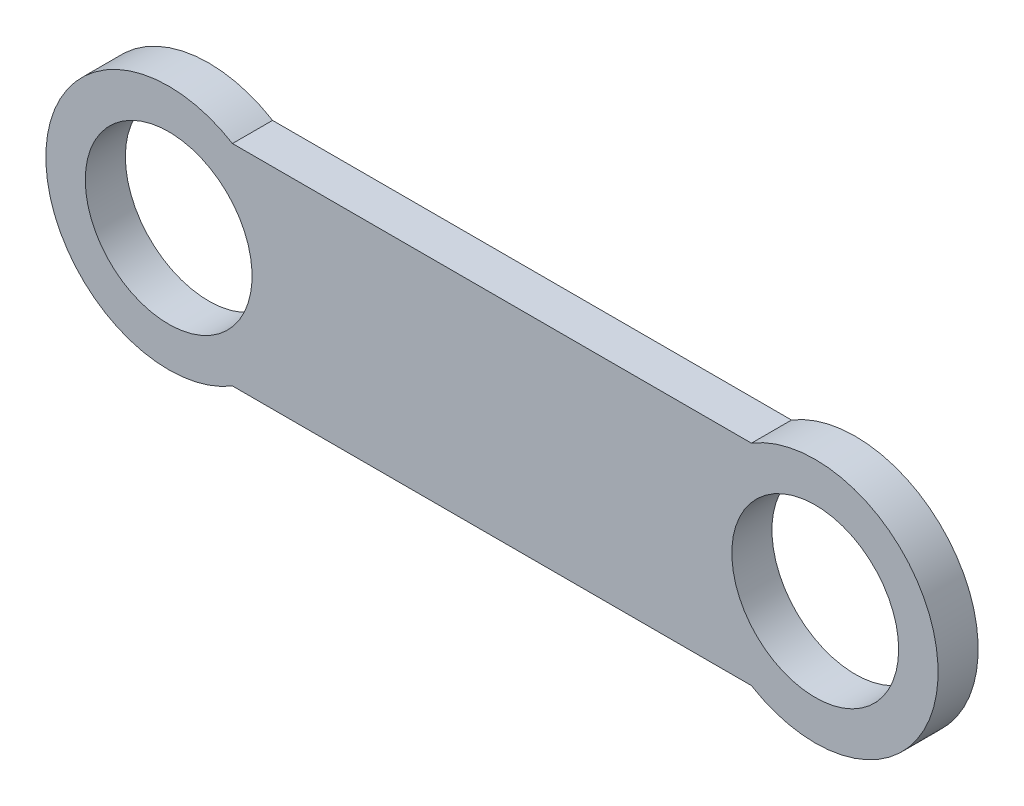
SolidWorks part; units mm, degrees
material "Teak"
ref_plane "Front Plane" through (0, 0, 0) normal (0, 0, 1) x (1, 0, 0)
ref_plane "Top Plane" through (0, 0, 0) normal (0, 1, 0) x (1, 0, 0)
ref_plane "Right Plane" through (0, 0, 0) normal (1, 0, 0) x (0, 0, -1)
sketch "Sketch1" plane through (0, 0, 0) normal (0, 0, 1) x (1, 0, 0)
  line L0 (-85.94, 0) -> (85.94, 0) construction
  line L1 (0, -39.678) -> (0, 39.678) construction
  line L2 (-20.0665, 8.1185) -> (20.0665, 8.1185)
  line L3 (-20.0665, -8.1185) -> (20.0665, -8.1185)
  circle A0 centre (25, 0) radius 6.45
  arc A1 (20.0665, 8.1185) -> (20.0665, -8.1185) centre (25, 0) cw
  arc A2 (-20.0665, 8.1185) -> (-20.0665, -8.1185) centre (-25, 0) ccw
  circle A3 centre (-25, 0) radius 6.45
  point P8 (0, 8.1185)
  point P12 (0, 0)
  point P16 (0, -8.1185)
  dimension "D1" = 9.5
  dimension "D2" = 12.9
  dimension "D3" = 50
extrude "Boss-Extrude1" add sketch "Sketch1" along normal blind 3.1 contours L2 A1 L3 A2
equation "\"p\"= 20mm"
equation "\"m\"= 1"
equation "\"hole_diam\"= 4mm"
equation "\"len_grip_1\" = 50mm"
equation "\"len_grip_2\" = 50mm"
equation "\"thick\" = 3.1mm"
equation "\"thick2\" = 20mm"
equation "\"wrist_cont_bearing_diam\"=3in"
equation "\"wrist_cont_bearing_thick\"=5/16in"
equation "\"len_forearm\" = 300mm"
equation "\"wrist_bearing_diam\"=3in"
equation "\"len_link\" = 7cm"
equation "\"elbow_cont_bearing_diam\"=10cm"
equation "\"elbow_cont_bearing2_diam\"=7.5cm"
equation "\"small_bearing_outer\"=13mm"
equation "\"servo1_L\"=40.7mm"
equation "\"servo1_W\"=20.5mm"
equation "\"servo1_H\"=43.5mm"
equation "\"servo1_hL\"=49mm"
equation "\"servo1_hW\"=10mm"
equation "\"D1@Sketch1\"=\"small_bearing_outer\"/2 + 3"
equation "\"D1@Boss-Extrude1\"=\"thick\""
